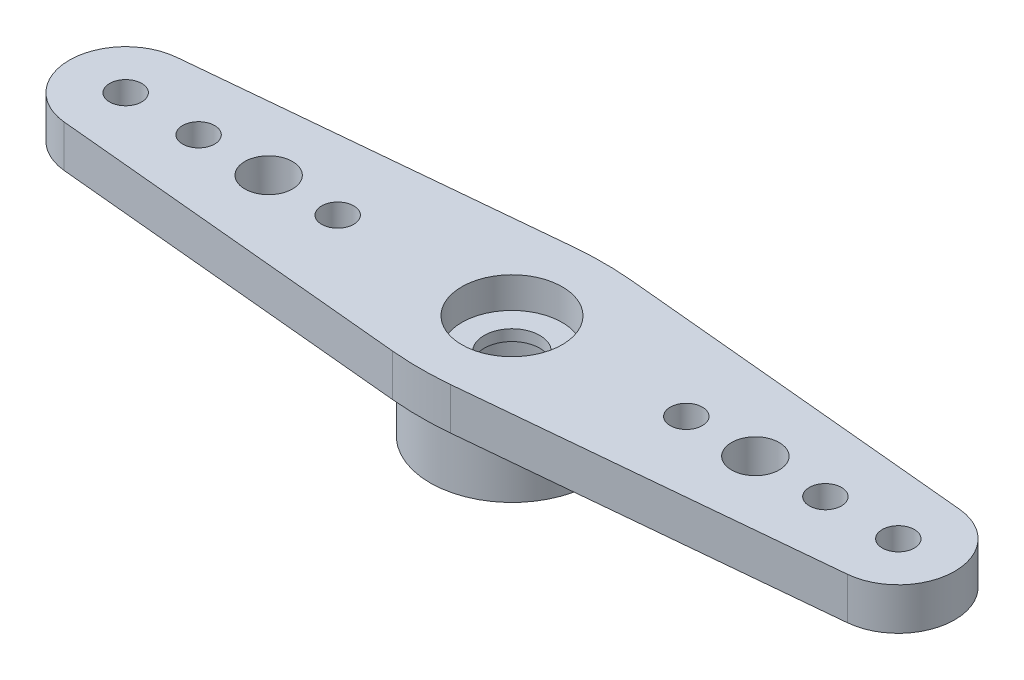
SolidWorks part; units mm, degrees
other "Markup1"
sketch "Sketch4" plane through (18.1928, 4.2672, 3.7665) normal (0.4235, 0.8352, 0.3507) x (0.7651, -0.1225, -0.6321)
other "Markup2"
sketch "Sketch5" plane through (18.1928, 4.2672, 3.7665) normal (0.4235, 0.8352, 0.3507) x (0.7651, -0.1225, -0.6321)
ref_plane "Front Plane" through (0, 0, 0) normal (0, 0, 1) x (1, 0, 0)
ref_plane "Top Plane" through (0, 0, 0) normal (0, 1, 0) x (1, 0, 0)
ref_plane "Right Plane" through (0, 0, 0) normal (1, 0, 0) x (0, 0, -1)
sketch "Sketch1" plane through (0, 0, 0) normal (0, 1, 0) x (1, 0, 0)
  circle A0 centre (0, 0) radius 3.3655
  circle A1 centre (0, 0) radius 2.2352
  dimension "D1" = 6.731
  dimension "D2" = 4.4704
extrude "Boss-Extrude1" add sketch "Sketch1" along normal blind 2.54
sketch "Sketch2" plane through (0, 2.54, 0) normal (0, 1, 0) x (1, 0, 0)
  line L0 (0, 0) -> (50000, 0) construction
  line L1 (0, 0) -> (0, 50000) construction
  line L2 (0, 3.8227) -> (16.0923, 2.3075)
  line L3 (0, -3.8227) -> (16.0923, -2.3075)
  line L4 (0, -3.8227) -> (-16.0923, -2.3075)
  line L5 (0, 3.8227) -> (-16.0923, 2.3075)
  circle A0 centre (15.875, 0) radius 0.6604
  circle A1 centre (12.8778, 0) radius 0.6604
  circle A2 centre (9.8806, 0) radius 0.6604
  circle A3 centre (7.1628, 0) radius 0.6604
  circle A4 centre (15.875, 0) radius 2.3178
  circle A5 centre (0, 0) radius 3.8227
  circle A6 centre (-15.875, 0) radius 2.3178
  circle A7 centre (-7.1628, 0) radius 0.6604
  circle A8 centre (-9.8806, 0) radius 0.6604
  circle A9 centre (-12.8778, 0) radius 0.6604
  circle A10 centre (-15.875, 0) radius 0.6604
  circle A11 centre (0, 0) radius 1.143
  circle M1 centre (0, 0) radius 3.3655
  circle M2 centre (0, 0) radius 2.2352
  dimension "D1" = 1.3208
  dimension "D6" = 4.6355
  dimension "D7" = 7.6454
  dimension "D8" = 2.286
  dimension "D2" = 15.875
  dimension "D3" = 2.9972
  dimension "D4" = 5.9944
  dimension "D5" = 8.7122
extrude "Boss-Extrude2" add sketch "Sketch2" along normal blind 1.7272 contours L5 A6 L4 A5 A8 A7 A9 | A6 A10 | A5 L3 A4 L2 A1 A2 A3 | A4 A0 | M1 M2 | L3 A5 L2 L5 L4 M1 | A11 M2
fillet "Fillet1" radius 12.7 2 edges at (0, 3.4036, -3.8227) (0, 3.4036, 3.8227)
sketch "Sketch3" plane through (0, 4.2672, 0) normal (0, 1, 0) x (1, 0, 0)
  circle A0 centre (0, 0) radius 2.0638
  circle M17 centre (0, 0) radius 1.143
  dimension "D1" = 4.1275
extrude "Cut-Extrude1" cut sketch "Sketch3" against normal blind 1.27 contours A0 M17
sketch "Sketch6" plane through (0, 4.2672, 0) normal (0, 1, 0) x (1, 0, 0)
  circle A0 centre (-12.8778, 0) radius 1
  circle A1 centre (12.8778, 0) radius 1
  dimension "D1" = 2
extrude "Cut-Extrude2" [suppressed] cut sketch "Sketch6" against normal up to next
sketch "Sketch7" plane through (0, 2.54, 0) normal (0, -1, 0) x (1, 0, 0)
  line L0 (0, 0) -> (0, -7.2908) construction
  circle A0 centre (10.325, 0) radius 1
  circle A1 centre (-10.325, 0) radius 1
  dimension "D1" = 2
  dimension "D2" = 10.325
extrude "Cut-Extrude3" [suppressed] cut sketch "Sketch7" against normal through all
sketch "Sketch8" plane through (0, 4.2672, 0) normal (0, 1, 0) x (1, 0, 0)
  line L0 (0, 0) -> (0, 6.8099) construction
  circle A0 centre (10, 0) radius 0.98
  circle A1 centre (0, 0) radius 1.143 construction
  circle A2 centre (-10, 0) radius 0.98
  dimension "D1" = 1.96
  dimension "D2" = 10
extrude "Cut-Extrude4" cut sketch "Sketch8" against normal through all
